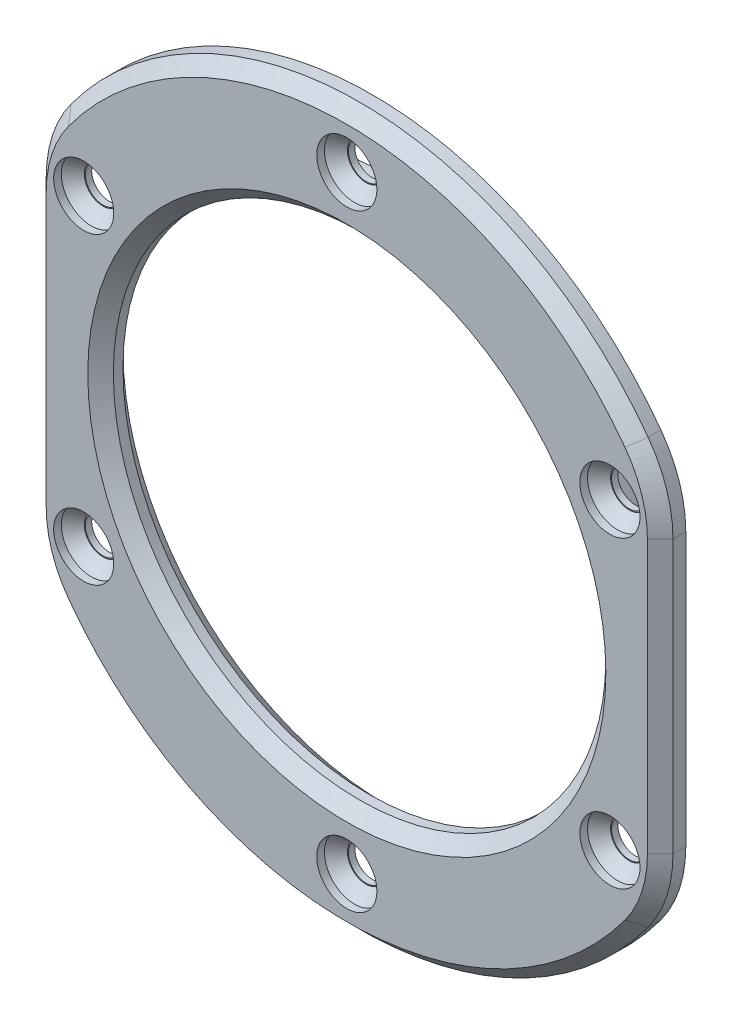
SolidWorks part; units mm, degrees
ref_plane "Front Plane" through (0, 0, 0) normal (0, 0, 1) x (1, 0, 0)
ref_plane "Top Plane" through (0, 0, 0) normal (0, 1, 0) x (1, 0, 0)
ref_plane "Right Plane" through (0, 0, 0) normal (1, 0, 0) x (0, 0, -1)
sketch "Sketch1" plane through (0, 0, 0) normal (0, 0, 1) x (1, 0, 0)
  circle A0 centre (0, 0) radius 19.25
  circle A1 centre (0, 0) radius 28
  dimension "D1" = 38.5
  dimension "D2" = 56
extrude "Boss-Extrude1" add sketch "Sketch1" along normal blind 2
sketch "Sketch2" plane through (0, 0, 0) normal (0, 0, -1) x (-1, 0, 0)
  circle A0 centre (0, 0) radius 19.25
  circle A1 centre (0, 0) radius 22.15
  circle A2 centre (0, 0) radius 19.25 construction
  dimension "D1" = 44.3
extrude "Boss-Extrude2" add sketch "Sketch2" along normal blind 1
sketch "Sketch3" plane through (0, 0, 2) normal (0, 0, 1) x (1, 0, 0)
  circle A0 centre (0, 23.75) radius 1.375
  circle A1 centre (20.5681, 11.875) radius 1.375
  circle A2 centre (20.5681, -11.875) radius 1.375
  circle A3 centre (0, -23.75) radius 1.375
  circle A4 centre (-20.5681, -11.875) radius 1.375
  circle A5 centre (-20.5681, 11.875) radius 1.375
  circle A6 centre (0, 0) radius 23.75 construction
  point P14 (0, 0)
  dimension "D2" = 2.75
  dimension "D3" = 47.5
  dimension "D1" = 6
extrude "Cut-Extrude1" cut sketch "Sketch3" against normal through all
sketch "Sketch4" plane through (0, 0, 2) normal (0, 0, 1) x (1, 0, 0)
  line L0 (0, 37.6944) -> (0, -37.3588) construction
  line L1 (24.5, 26.7836) -> (24.5, -27.4399)
  line L2 (-37.3946, 26.7836) -> (-24.5, 26.7836)
  line L3 (-37.3946, 26.7836) -> (-37.3946, -27.4399)
  line L4 (-37.3946, -27.4399) -> (-24.5, -27.4399)
  line L5 (-24.5, 26.7836) -> (-24.5, -27.4399)
  line L6 (37.3946, -27.4399) -> (24.5, -27.4399)
  line L7 (37.3946, 26.7836) -> (37.3946, -27.4399)
  line L8 (37.3946, 26.7836) -> (24.5, 26.7836)
  dimension "D1" = 49
extrude "Cut-Extrude2" cut sketch "Sketch4" against normal through all
fillet "Fillet1" radius 10 4 edges at (24.5, -13.5554, 1) (24.5, 13.5554, 1) (-24.5, 13.5554, 1) (-24.5, -13.5554, 1)
sketch "Sketch5" plane through (0, 0, 2) normal (0, 0, 1) x (1, 0, 0)
  circle A0 centre (0, 23.75) radius 2.35
  circle A1 centre (20.5681, 11.875) radius 2.35
  circle A2 centre (-20.5681, 11.875) radius 2.35
  circle A3 centre (20.5681, -11.875) radius 2.35
  circle A4 centre (0, -23.75) radius 2.35
  circle A5 centre (-20.5681, -11.875) radius 2.35
  dimension "D1" = 4.7
extrude "Cut-Extrude3" cut sketch "Sketch5" against normal blind 1.5
chamfer "Chamfer2" distance 0.9 angle 45 6 edges at (-18.2181, -11.875, 0.5) (2.35, -23.75, 0.5) (22.9181, -11.875, 0.5) (22.9181, 11.875, 0.5) (2.35, 23.75, 0.5) (-18.2181, 11.875, 0.5)
chamfer "Chamfer1" distance 1 angle 45 9 edges at (0, -28, 2) (24.0015, -13.7834, 2) (-24.0015, -13.7834, 2) (24.5, 0, 2) (-24.5, 0, 2) (24.0015, 13.7834, 2) (-24.0015, 13.7834, 2) (0, 28, 2) (19.25, 0, 2)
chamfer "Chamfer3" distance 1.25 angle 45 1 edges at (-19.25, 0, -1)
